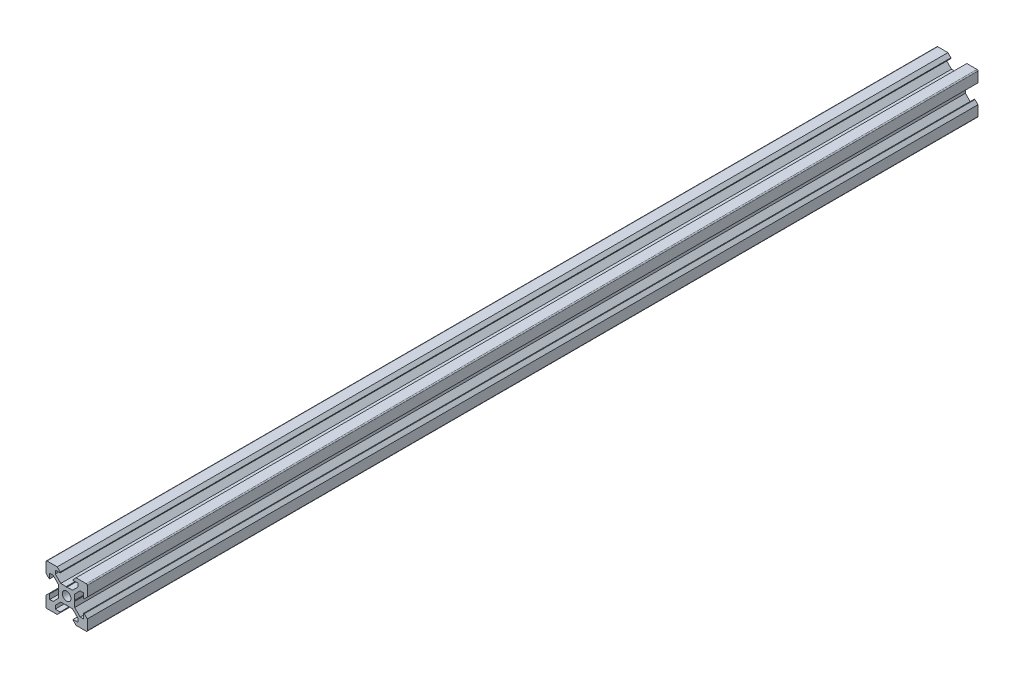
SolidWorks part; units mm, degrees
material "6061-T6 (SS)"
ref_plane "Front Plane" through (0, 0, 0) normal (0, 0, 1) x (1, 0, 0)
ref_plane "Top Plane" through (0, 0, 0) normal (0, 1, 0) x (1, 0, 0)
ref_plane "Right Plane" through (0, 0, 0) normal (1, 0, 0) x (0, 0, -1)
ref_plane "Plane1" through (0, 0, 0) normal (0, 0, -1) x (-1, 0, 0)
sketch "Sketch1" plane through (0, 0, 0) normal (0, 0, -1) x (-1, 0, 0)
  line L0 (-3.9, -0.21) -> (-3.9, -2.8393)
  line L1 (-3.9, -2.8393) -> (-6.5607, -5.5)
  line L2 (-6.5607, -5.5) -> (-8.2, -5.5)
  line L3 (-8.2, -5.5) -> (-8.2, -3.125)
  line L4 (-8.2, -3.125) -> (-8.545, -3.125)
  line L5 (-8.545, -3.125) -> (-10, -4.58)
  line L6 (-10, -4.58) -> (-10, -9.5)
  line L7 (-9.5, -10) -> (-4.58, -10)
  line L8 (-4.58, -10) -> (-3.125, -8.545)
  line L9 (-3.125, -8.545) -> (-3.125, -8.2)
  line L10 (-3.125, -8.2) -> (-5.5, -8.2)
  line L11 (-5.5, -8.2) -> (-5.5, -6.5607)
  line L12 (-5.5, -6.5607) -> (-2.8393, -3.9)
  line L13 (-2.8393, -3.9) -> (-0.21, -3.9)
  line L14 (-0.21, -3.9) -> (0, -3.69)
  line L15 (0, -3.69) -> (0.21, -3.9)
  line L16 (0.21, -3.9) -> (2.8393, -3.9)
  line L17 (2.8393, -3.9) -> (5.5, -6.5607)
  line L18 (5.5, -6.5607) -> (5.5, -8.2)
  line L19 (5.5, -8.2) -> (3.125, -8.2)
  line L20 (3.125, -8.2) -> (3.125, -8.545)
  line L21 (3.125, -8.545) -> (4.58, -10)
  line L22 (4.58, -10) -> (9.5, -10)
  line L23 (10, -9.5) -> (10, -4.58)
  line L24 (10, -4.58) -> (8.545, -3.125)
  line L25 (8.545, -3.125) -> (8.2, -3.125)
  line L26 (8.2, -3.125) -> (8.2, -5.5)
  line L27 (8.2, -5.5) -> (6.5607, -5.5)
  line L28 (6.5607, -5.5) -> (3.9, -2.8393)
  line L29 (3.9, -2.8393) -> (3.9, -0.21)
  line L30 (3.9, -0.21) -> (3.69, 0)
  line L31 (3.69, 0) -> (3.9, 0.21)
  line L32 (3.9, 0.21) -> (3.9, 2.8393)
  line L33 (3.9, 2.8393) -> (6.5607, 5.5)
  line L34 (6.5607, 5.5) -> (8.2, 5.5)
  line L35 (8.2, 5.5) -> (8.2, 3.125)
  line L36 (8.2, 3.125) -> (8.545, 3.125)
  line L37 (8.545, 3.125) -> (10, 4.58)
  line L38 (10, 4.58) -> (10, 9.5)
  line L39 (9.5, 10) -> (4.58, 10)
  line L40 (4.58, 10) -> (3.125, 8.545)
  line L41 (3.125, 8.545) -> (3.125, 8.2)
  line L42 (3.125, 8.2) -> (5.5, 8.2)
  line L43 (5.5, 8.2) -> (5.5, 6.5607)
  line L44 (5.5, 6.5607) -> (2.8393, 3.9)
  line L45 (2.8393, 3.9) -> (0.21, 3.9)
  line L46 (0.21, 3.9) -> (0, 3.69)
  line L47 (0, 3.69) -> (-0.21, 3.9)
  line L48 (-0.21, 3.9) -> (-2.8393, 3.9)
  line L49 (-2.8393, 3.9) -> (-5.5, 6.5607)
  line L50 (-5.5, 6.5607) -> (-5.5, 8.2)
  line L51 (-5.5, 8.2) -> (-3.125, 8.2)
  line L52 (-3.125, 8.2) -> (-3.125, 8.545)
  line L53 (-3.125, 8.545) -> (-4.58, 10)
  line L54 (-4.58, 10) -> (-9.5, 10)
  line L55 (-10, 9.5) -> (-10, 4.58)
  line L56 (-10, 4.58) -> (-8.545, 3.125)
  line L57 (-8.545, 3.125) -> (-8.2, 3.125)
  line L58 (-8.2, 3.125) -> (-8.2, 5.5)
  line L59 (-8.2, 5.5) -> (-6.5607, 5.5)
  line L60 (-6.5607, 5.5) -> (-3.9, 2.8393)
  line L61 (-3.9, 2.8393) -> (-3.9, 0.21)
  line L62 (-3.9, 0.21) -> (-3.69, 0)
  line L63 (-3.69, 0) -> (-3.9, -0.21)
  circle A0 centre (0, 0) radius 2.1
  arc A1 (-10, -9.5) -> (-9.5, -10) centre (-9.5, -9.5) ccw
  arc A2 (9.5, -10) -> (10, -9.5) centre (9.5, -9.5) ccw
  arc A3 (10, 9.5) -> (9.5, 10) centre (9.5, 9.5) ccw
  arc A4 (-9.5, 10) -> (-10, 9.5) centre (-9.5, 9.5) ccw
extrude "Boss-Extrude1" add sketch "Sketch1" against normal blind 500
cosmetic thread "Cosmetic Thread1" parameters "D1"=12.7, "D2"=5
ref_plane "cut plane" through (0, 0, 68.2) normal (0, 0, 1) x (1, 0, 0)
split "Split1" trim tools "cut plane" bodies to split 103 resulting bodies 105
hole_wizard "M5x0.8 Tapped Hole1" positions "Sketch4" profile "Sketch5" tap size "M5x0.8" standard "ANSI Metric"
sketch "Sketch4" plane through (0, 0, 500) normal (0, 0, 1) x (1, 0, 0)
  point P0 (0, 0)
sketch "Sketch5" plane through (0, 0, 500) normal (1, 0, 0) x (0, -1, 0)
  line L0 (0, 0) -> (0, 15.2318)
  line L1 (0, 15.2318) -> (2.1, 13.97)
  line L2 (2.1, 13.97) -> (2.1, 0)
  line L5 (2.1, 0) -> (0, 0)
  line L10 (0, 15.2318) -> (-2.1, 13.97) construction
  line L11 (0, -6.35) -> (0, 107.95) construction
  dimension "Tap Drill Dia." = 4.2
  dimension "Tap Drill Depth" = 13.97
  dimension "Drill Angle" = 118
hole_wizard "M5x0.8 Tapped Hole2" positions "Sketch7" profile "Sketch6" tap size "M5x0.8" standard "ANSI Metric"
sketch "Sketch7" plane through (0, 0, 68.2) normal (0, 0, -1) x (-1, 0, 0)
  point P0 (0, 0)
sketch "Sketch6" plane through (0, 0, 68.2) normal (1, 0, 0) x (0, 1, 0)
  line L0 (0, 0) -> (0, 15.2318)
  line L1 (0, 15.2318) -> (2.1, 13.97)
  line L2 (2.1, 13.97) -> (2.1, 0)
  line L5 (2.1, 0) -> (0, 0)
  line L10 (0, 15.2318) -> (-2.1, 13.97) construction
  line L11 (0, -6.35) -> (0, 107.95) construction
  dimension "Tap Drill Dia." = 4.2
  dimension "Tap Drill Depth" = 13.97
  dimension "Drill Angle" = 118
